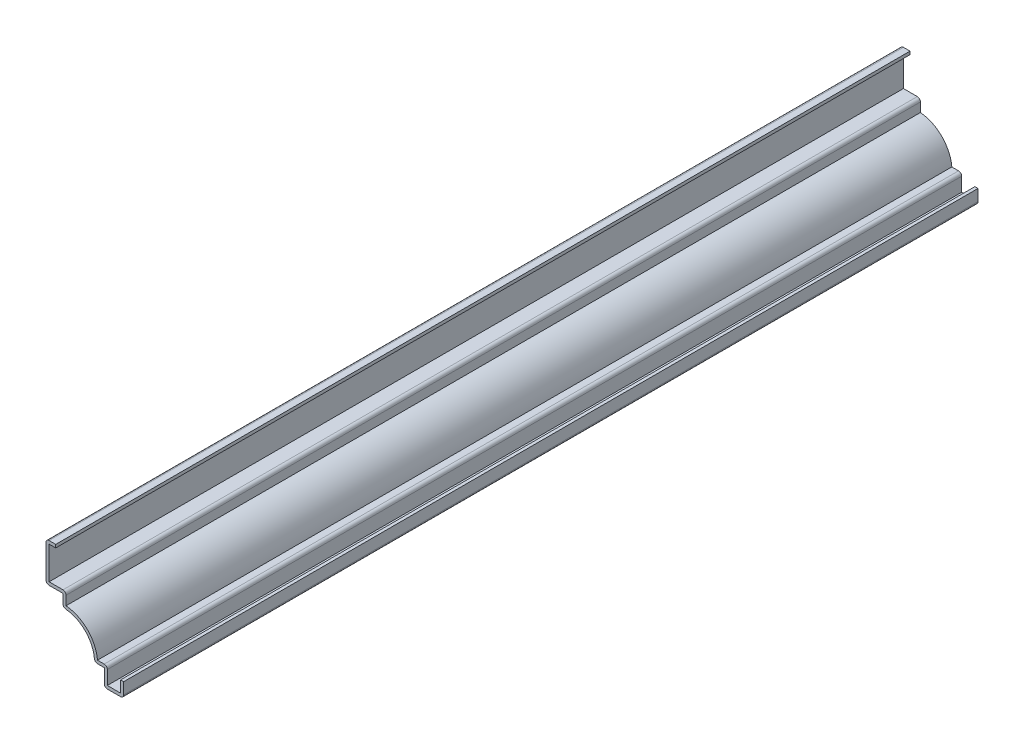
SolidWorks part; units mm, degrees
ref_plane "Front Plane" through (0, 0, 0) normal (0, 0, 1) x (1, 0, 0)
ref_plane "Top Plane" through (0, 0, 0) normal (0, 1, 0) x (1, 0, 0)
ref_plane "Right Plane" through (0, 0, 0) normal (1, 0, 0) x (0, 0, -1)
sketch "Sketch1" plane through (0, 0, 0) normal (0, 0, 1) x (1, 0, 0)
  line L0 (0, 4.7625) -> (0, 0)
  line L1 (0, 0) -> (-6.35, 0)
  line L2 (-6.35, 0) -> (-6.35, 5.5562)
  line L3 (-6.35, 5.5562) -> (-9.525, 5.5562)
  line L4 (-19.8438, 15.875) -> (-19.8438, 19.8437)
  line L5 (-19.8438, 19.8437) -> (-25.4, 19.8438)
  line L6 (-25.4, 19.8438) -> (-25.4, 32.5437)
  line L7 (-25.4, 32.5437) -> (-22.225, 32.5437)
  arc A0 (-9.525, 5.5562) -> (-19.8438, 15.875) centre (-19.8438, 5.5562) ccw
  point P8 (-11.7945, 5.5562)
  dimension "D1" = 10.3187
  dimension "D2" = 6.35
  dimension "D3" = 4.7625
  dimension "D4" = 5.5562
  dimension "D5" = 19.8438
  dimension "D6" = 3.9687
  dimension "D7" = 3.175
  dimension "D8" = 12.7
  dimension "D9" = 3.175
  dimension "D10" = 22.225
extrude "Extrude-Thin1" add sketch "Sketch1" against normal blind 279.4 thin
fillet "Fillet1" radius 1.016 8 edges at (0, 0, -139.7) (-6.35, 0, -139.7) (-5.334, 6.5722, -139.7) (-9.525, 5.5562, -139.7) (-19.8438, 15.875, -139.7) (-18.8278, 20.8597, -139.7) (-25.4, 19.8438, -139.7) (-25.4, 32.5437, -139.7)
equation "\"D1@Extrude-Thin1\"=11"
